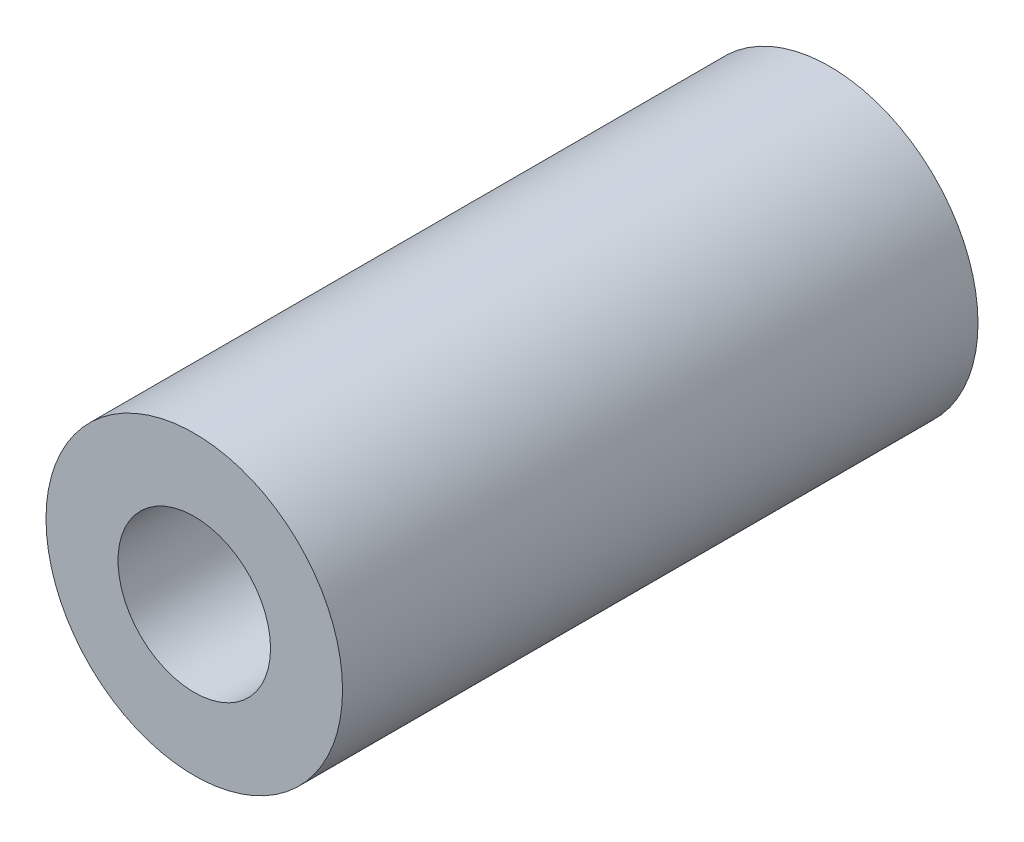
SolidWorks part; units mm, degrees
material "PBT Uniwersalny"
ref_plane "Płaszczyzna przednia" through (0, 0, 0) normal (0, 0, 1) x (1, 0, 0)
ref_plane "Płaszczyzna górna" through (0, 0, 0) normal (0, 1, 0) x (1, 0, 0)
ref_plane "Płaszczyzna prawa" through (0, 0, 0) normal (1, 0, 0) x (0, 0, -1)
sketch "Szkic1" plane through (0, 0, 0) normal (0, 0, 1) x (1, 0, 0)
  circle A1 centre (0, 0) radius 1.8
  circle A2 centre (0, 0) radius 3.5
  dimension "D2" = 3.6
  dimension "D1" = 7
extrude "Dodanie-wyciągnięcie1" add sketch "Szkic1" along normal blind 15
